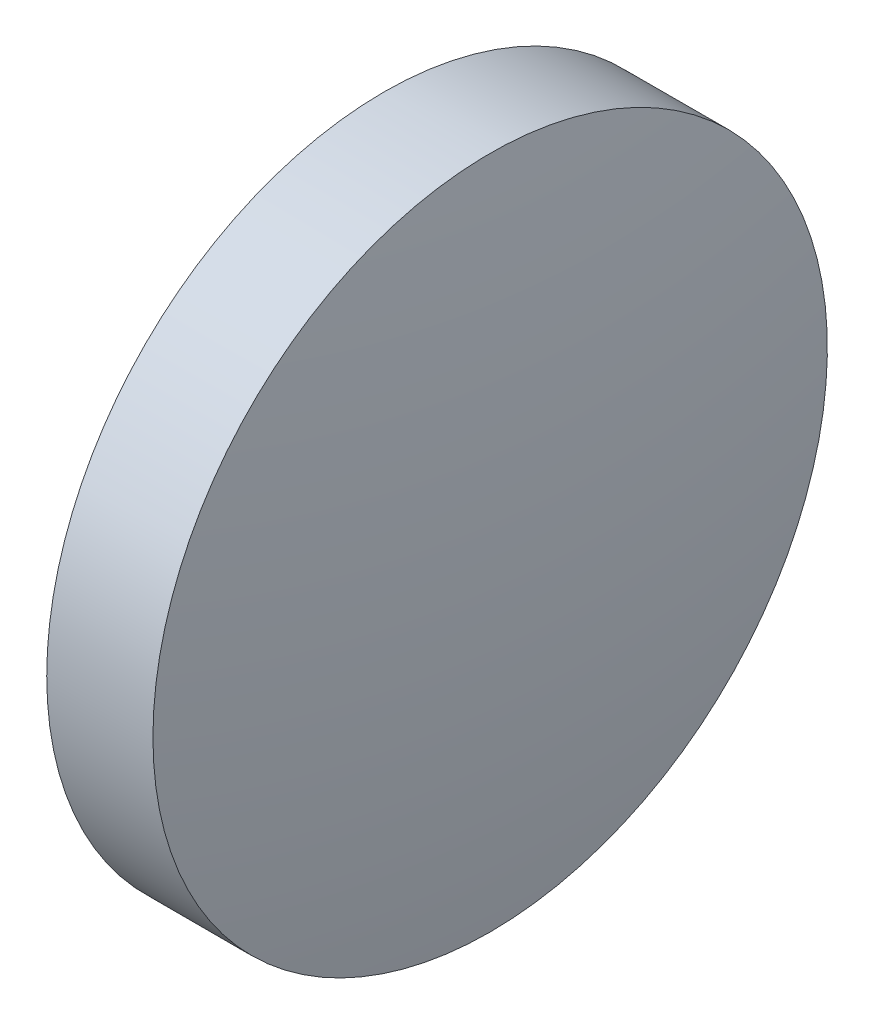
SolidWorks part; units mm, degrees
ref_plane "前视基准面" through (0, 0, 0) normal (0, 0, 1) x (1, 0, 0)
ref_plane "上视基准面" through (0, 0, 0) normal (0, 1, 0) x (1, 0, 0)
ref_plane "右视基准面" through (0, 0, 0) normal (1, 0, 0) x (0, 0, -1)
sketch "草图1" plane through (0, 0, 0) normal (0, 0, 1) x (1, 0, 0)
  line L0 (39.6527, 24.3081) -> (46.7386, 24.3081) construction
  line L1 (42.2291, 30.6581) -> (44.2291, 30.6581)
  line L2 (44.2291, 30.6581) -> (44.2291, 17.9581)
  line L3 (44.2291, 17.9581) -> (42.2291, 17.9581)
  line L4 (42.2291, 17.9581) -> (42.2291, 30.6581)
  arc A0 (42.2291, 30.6581) -> (42.2291, 17.9581) centre (82.3046, 24.3081) ccw
  arc A1 (44.2291, 17.9581) -> (44.2291, 30.6581) centre (4.1536, 24.3081) ccw
  dimension "D1" = 12.7
revolve "旋转1" add sketch "草图1" angle 360 about L0
